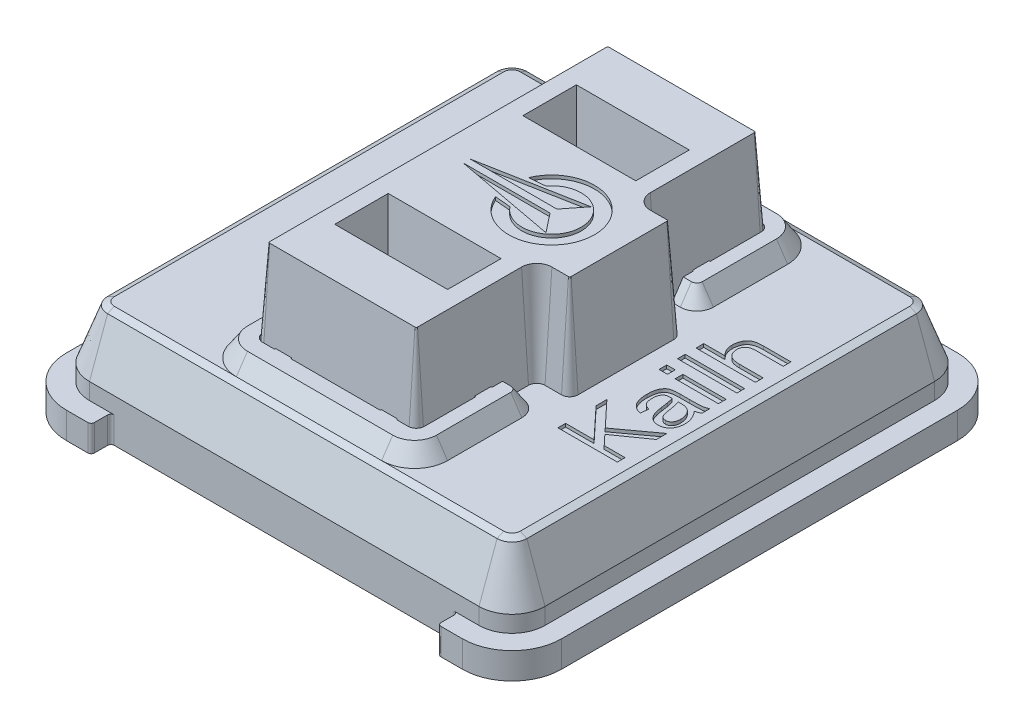
SolidWorks part; units mm, degrees
material "Plastique personnalisé"
ref_plane "Front Plane" through (0, 0, 0) normal (0, 0, 1) x (1, 0, 0)
ref_plane "Top Plane" through (0, 0, 0) normal (0, 1, 0) x (1, 0, 0)
ref_plane "Right Plane" through (0, 0, 0) normal (1, 0, 0) x (0, 0, -1)
sketch "Sketch1" plane through (0, 0, 0) normal (0, 1, 0) x (1, 0, 0)
  line L0 (-12.6999, -17.2743) -> (27.7413, -17.2743) construction
  line L1 (-6, 7.5) -> (6, 7.5)
  line L2 (-7.5, 6) -> (-7.5, -6)
  line L3 (-6, -7.5) -> (6, -7.5)
  line L4 (7.5, 6) -> (7.5, -6)
  line L5 (-7.5, 7.5) -> (7.5, -7.5) construction
  line L6 (-7.5, -7.5) -> (7.5, 7.5) construction
  arc A0 (-7.5, -6) -> (-6, -7.5) centre (-6, -6) ccw
  arc A1 (6, -7.5) -> (7.5, -6) centre (6, -6) ccw
  arc A2 (6, 7.5) -> (7.5, 6) centre (6, 6) cw
  arc A3 (-6, 7.5) -> (-7.5, 6) centre (-6, 6) ccw
  point P0 (0, 0)
  dimension "D3" = 1.5
  dimension "D1" = 15
  dimension "D2" = 15
sketch "Sketch5" plane through (0, 0, 0) normal (0, 1, 0) x (1, 0, 0)
  line L1 (6, -7.5) -> (-6, -7.5)
  line L2 (7.5, -6) -> (7.5, 6)
  line L3 (6, 7.5) -> (-6, 7.5)
  line L4 (-7.5, -6) -> (-7.5, 6)
  line L5 (7.5, -7.5) -> (-7.5, 7.5) construction
  line L6 (7.5, 7.5) -> (-7.5, -7.5) construction
  arc A0 (-6, -7.5) -> (-7.5, -6) centre (-6, -6) cw
  arc A1 (6, -7.5) -> (7.5, -6) centre (6, -6) ccw
  arc A2 (7.5, 6) -> (6, 7.5) centre (6, 6) ccw
  arc A3 (-6, 7.5) -> (-7.5, 6) centre (-6, 6) ccw
  point P0 (0, 0)
  dimension "D1" = 1.5
extrude "Boss-Extrude4" add sketch "Sketch5" along normal mid plane 0.8
sketch "Sketch6" plane through (0, 0.4, 0) normal (0, 1, 0) x (1, 0, 0)
  line L0 (-7.5, 7.5) -> (7.5, -7.5) construction
  line L1 (5.9, -6.9) -> (-5.9, -6.9)
  line L2 (6.9, -5.9) -> (6.9, 5.9)
  line L3 (5.9, 6.9) -> (-5.9, 6.9)
  line L4 (-6.9, -5.9) -> (-6.9, 5.9)
  line L5 (6.9, -6.9) -> (-6.9, 6.9) construction
  line L6 (6.9, 6.9) -> (-6.9, -6.9) construction
  arc A0 (-5.9, -6.9) -> (-6.9, -5.9) centre (-5.9, -5.9) cw
  arc A1 (5.9, -6.9) -> (6.9, -5.9) centre (5.9, -5.9) ccw
  arc A2 (6.9, 5.9) -> (5.9, 6.9) centre (5.9, 5.9) ccw
  arc A3 (-5.9, 6.9) -> (-6.9, 5.9) centre (-5.9, 5.9) ccw
  point P0 (0, 0)
  dimension "D2" = 1
  dimension "D1" = 13.8
extrude "Boss-Extrude5" add sketch "Sketch6" along normal blind 0.5
sketch "Sketch7" plane through (0, 0.9, 0) normal (0, 1, 0) x (1, 0, 0)
  line L4 (-5.9, -6.9) -> (5.9, -6.9)
  line L5 (6.9, -5.9) -> (6.9, 5.9)
  line L6 (5.9, 6.9) -> (-5.9, 6.9)
  line L7 (-6.9, 5.9) -> (-6.9, -5.9)
  line L8 (-5.9, -6.9) -> (5.9, -6.9)
  line L9 (6.9, -5.9) -> (6.9, 5.9)
  line L10 (5.9, 6.9) -> (-5.9, 6.9)
  line L11 (-6.9, 5.9) -> (-6.9, -5.9)
  arc A4 (-6.9, -5.9) -> (-5.9, -6.9) centre (-5.9, -5.9) ccw
  arc A5 (5.9, -6.9) -> (6.9, -5.9) centre (5.9, -5.9) ccw
  arc A6 (6.9, 5.9) -> (5.9, 6.9) centre (5.9, 5.9) ccw
  arc A7 (-5.9, 6.9) -> (-6.9, 5.9) centre (-5.9, 5.9) ccw
  arc A8 (-6.9, -5.9) -> (-5.9, -6.9) centre (-5.9, -5.9) ccw
  arc A9 (5.9, -6.9) -> (6.9, -5.9) centre (5.9, -5.9) ccw
  arc A10 (6.9, 5.9) -> (5.9, 6.9) centre (5.9, 5.9) ccw
  arc A11 (-5.9, 6.9) -> (-6.9, 5.9) centre (-5.9, 5.9) ccw
  arc M9 (-6.9, -5.9) -> (-5.9, -6.9) centre (-5.9, -5.9) ccw
  line M10 (-5.9, -6.9) -> (5.9, -6.9)
  arc M11 (5.9, -6.9) -> (6.9, -5.9) centre (5.9, -5.9) ccw
  line M12 (6.9, -5.9) -> (6.9, 5.9)
  arc M13 (6.9, 5.9) -> (5.9, 6.9) centre (5.9, 5.9) ccw
  line M14 (5.9, 6.9) -> (-5.9, 6.9)
  arc M15 (-5.9, 6.9) -> (-6.9, 5.9) centre (-5.9, 5.9) ccw
  line M16 (-6.9, 5.9) -> (-6.9, -5.9)
  dimension "D1" = 0
extrude "Boss-Extrude6" add sketch "Sketch7" along normal offset from surface 2.5 draft 20 contours M16 M9 M10 M11 M12 M13 M14 M15
chamfer "Chamfer1" distance 0.1 angle 45 8 edges at (0, 2.5, -6.3176) (6.1953, 2.5, -6.1953) (6.3176, 2.5, 0) (6.1953, 2.5, 6.1953) (0, 2.5, 6.3176) (-6.1953, 2.5, 6.1953) (-6.3176, 2.5, 0) (-6.1953, 2.5, -6.1953)
sketch "Sketch8" plane through (0, 2.5, 0) normal (0, 1, 0) x (1, 0, 0)
  line L0 (5.9, 6.1503) -> (-5.9, 6.1503) construction
  line L1 (2.2, -6.1503) -> (-2.2, -6.1503)
  line L2 (3.2, -5.1503) -> (3.2, -2.9003)
  line L3 (2.2, 6.1503) -> (-2.2, 6.1503)
  line L4 (-3.2, -5.1503) -> (-3.2, 5.1503)
  line L5 (3.2, -6.1503) -> (-3.2, 6.1503) construction
  line L6 (3.2, 6.1503) -> (-3.2, -6.1503) construction
  line L7 (2.7, 2.4003) -> (2.3, 2.4003)
  line L8 (2.3, 2.4003) -> (2.3, -2.4003)
  line L9 (2.3, -2.4003) -> (2.7, -2.4003)
  line L10 (3.2, 2.9003) -> (3.2, 5.1503)
  arc A0 (-2.2, -6.1503) -> (-3.2, -5.1503) centre (-2.2, -5.1503) cw
  arc A1 (2.2, -6.1503) -> (3.2, -5.1503) centre (2.2, -5.1503) ccw
  arc A2 (3.2, 5.1503) -> (2.2, 6.1503) centre (2.2, 5.1503) ccw
  arc A3 (-2.2, 6.1503) -> (-3.2, 5.1503) centre (-2.2, 5.1503) ccw
  arc A4 (2.7, -2.4003) -> (3.2, -2.9003) centre (2.7, -2.9003) cw
  arc A5 (2.7, 2.4003) -> (3.2, 2.9003) centre (2.7, 2.9003) ccw
  point P0 (0, 0)
  point P28 (3.2, 2.4003)
  dimension "D2" = 1
  dimension "D5" = 0.5
  dimension "D1" = 6.4
  dimension "D3" = 3.75
  dimension "D4" = 0.9
extrude "Boss-Extrude7" add sketch "Sketch8" along normal blind 0.5 draft 34
sketch "Sketch9" plane through (0, 2.5, 0) normal (0, 1, 0) x (1, 0, 0)
  line L1 (-2.2, -5.35) -> (2.2, -5.35)
  line L2 (-2.45, -5.1) -> (-2.45, 5.1)
  line L3 (-2.2, 5.35) -> (2.2, 5.35)
  line L4 (2.45, -5.1) -> (2.45, 5.1)
  line L5 (-2.45, -5.35) -> (2.45, 5.35) construction
  line L6 (-2.45, 5.35) -> (2.45, -5.35) construction
  arc A0 (-2.2, -5.35) -> (-2.45, -5.1) centre (-2.2, -5.1) cw
  arc A1 (2.2, -5.35) -> (2.45, -5.1) centre (2.2, -5.1) ccw
  arc A2 (2.2, 5.35) -> (2.45, 5.1) centre (2.2, 5.1) cw
  arc A3 (-2.45, 5.1) -> (-2.2, 5.35) centre (-2.2, 5.1) cw
  point P0 (0, 0)
  dimension "D2" = 0.25
  dimension "D1" = 10.7
  dimension "D3" = 4.9
extrude "Cut-Extrude1" cut sketch "Sketch9" along normal through all
sketch "Sketch11" plane through (0, 2.5, 0) normal (0, 1, 0) x (1, 0, 0)
  line L0 (2.2, 5.35) -> (-2.2, 5.35) construction
  line L1 (2.45, 2.7376) -> (2.45, 5.1) construction
  line L2 (-2.45, 5.1) -> (-2.45, -5.1) construction
  line L3 (-2.2, -5.35) -> (2.2, -5.35) construction
  line L4 (2.45, -5.1) -> (2.45, -2.7376) construction
  line L5 (-1.8598, 5.35) -> (-1.3402, 5.35)
  line L6 (1.3402, 5.35) -> (1.8598, 5.35)
  line L7 (2.45, 3.5598) -> (2.45, 3.0402)
  line L8 (2.45, -3.0402) -> (2.45, -3.5598)
  line L9 (1.8598, -5.35) -> (1.3402, -5.35)
  line L10 (-1.3402, -5.35) -> (-1.8598, -5.35)
  line L11 (-2.45, -3.5598) -> (-2.45, -3.0402)
  line L12 (-2.45, 3.0402) -> (-2.45, 3.5598)
  line L13 (0, 0) -> (-1.4423, 0) construction
  line L14 (0, 0) -> (0, 1.7321) construction
  arc A0 (-1.8598, 5.35) -> (-1.3402, 5.35) centre (-1.6, 5.5) ccw
  arc A1 (1.3402, 5.35) -> (1.8598, 5.35) centre (1.6, 5.5) ccw
  arc A2 (2.45, 3.5598) -> (2.45, 3.0402) centre (2.6, 3.3) ccw
  arc A3 (-2.45, 3.5598) -> (-2.45, 3.0402) centre (-2.6, 3.3) cw
  arc A4 (-2.45, -3.0402) -> (-2.45, -3.5598) centre (-2.6, -3.3) cw
  arc A5 (-1.8598, -5.35) -> (-1.3402, -5.35) centre (-1.6, -5.5) cw
  arc A6 (1.3402, -5.35) -> (1.8598, -5.35) centre (1.6, -5.5) cw
  arc A7 (2.45, -3.0402) -> (2.45, -3.5598) centre (2.6, -3.3) ccw
  dimension "D1" = 0.3
  dimension "D2" = 0.15
  dimension "D3" = 1.6
  dimension "D4" = 3.3
extrude "Boss-Extrude8" add sketch "Sketch11" along normal up to surface (0.5 mm away) up to face at (0.7315, 3, 0)
sketch "Sketch12" plane through (0, 2.5, 0) normal (0, 1, 0) x (1, 0, 0)
  line L0 (2.7, 1.7) -> (3.2, 1.7)
  line L1 (2.2, 5.35) -> (-2.2, 5.35)
  line L2 (2.45, 5.1) -> (2.45, 1.95)
  line L3 (2.2, -5.35) -> (-2.2, -5.35)
  line L4 (-2.45, 5.1) -> (-2.45, -5.1)
  line L5 (2.45, 5.35) -> (-2.45, -5.35) construction
  line L6 (2.45, -5.35) -> (-2.45, 5.35) construction
  line L7 (3.45, 1.45) -> (3.45, -1.45)
  line L8 (3.2, -1.7) -> (2.7, -1.7)
  line L9 (2.45, -1.95) -> (2.45, -5.1)
  line L10 (-1.5, -2.25) -> (1.5, -3.45) construction
  line L11 (-1.5, -2.25) -> (1.5, -2.25)
  line L12 (-1.5, -2.25) -> (-1.5, -3.45)
  line L13 (-1.5, -3.45) -> (1.5, -3.45)
  line L14 (1.5, -2.25) -> (1.5, -3.45)
  line L15 (0, 0) -> (-1.3542, 0) construction
  line L16 (1.5, 2.25) -> (1.5, 3.45)
  line L17 (-1.5, 3.45) -> (1.5, 3.45)
  line L18 (-1.5, 2.25) -> (-1.5, 3.45)
  line L19 (-1.5, 2.25) -> (1.5, 2.25)
  arc A0 (-2.2, -5.35) -> (-2.45, -5.1) centre (-2.2, -5.1) cw
  arc A1 (2.45, -5.1) -> (2.2, -5.35) centre (2.2, -5.1) cw
  arc A2 (2.7, -1.7) -> (2.45, -1.95) centre (2.7, -1.95) ccw
  arc A3 (-2.2, 5.35) -> (-2.45, 5.1) centre (-2.2, 5.1) ccw
  arc A4 (2.2, 5.35) -> (2.45, 5.1) centre (2.2, 5.1) cw
  arc A5 (2.7, 1.7) -> (2.45, 1.95) centre (2.7, 1.95) cw
  arc A6 (3.2, 1.7) -> (3.45, 1.45) centre (3.2, 1.45) cw
  arc A7 (3.45, -1.45) -> (3.2, -1.7) centre (3.2, -1.45) cw
  point P0 (0, 0)
  point P18 (2.45, -1.7)
  point P29 (3.45, 1.7)
  point P32 (3.45, -1.7)
  point P37 (0, -2.85)
  dimension "D5" = 0.25
  dimension "D1" = 4.9
  dimension "D2" = 10.7
  dimension "D3" = 1
  dimension "D4" = 3.4
  dimension "D6" = 1.2
  dimension "D7" = 3
  dimension "D8" = 5.7
extrude "Boss-Extrude9" add sketch "Sketch12" along normal blind 3 draft 4
sketch "Sketch13" plane through (0, 2.5, 0) normal (0, 1, 0) x (1, 0, 0)
  line L0 (5.809, 2.994) -> (5.809, -2.994) construction
  line L1 (5.809, 0) -> (0, 0) construction
  text T0 "Kailh" font "@Arial Unicode MS" height 1.8
extrude "Cut-Extrude2" cut sketch "Sketch13" against normal blind 0.1
sketch "Sketch14" plane through (0, 5.5, 0) normal (0, 1, 0) x (1, 0, 0)
  line L0 (0, 0.5) -> (0.4816, 0.5421)
  line L1 (0, -0.5) -> (0.4816, -0.5421)
  line L2 (0, 0) -> (-1.6937, 0) construction
  line L3 (-1.377, 0.1043) -> (1.2556, 0.1043)
  line L4 (1.2556, 0.1043) -> (1.7122, 0.6819)
  line L5 (1.7122, 0.6819) -> (-1.377, 0.1043)
  line L6 (1.2556, -0.1043) -> (1.7122, -0.6819)
  line L7 (-1.377, -0.1043) -> (1.2556, -0.1043)
  line L8 (1.7122, -0.6819) -> (-1.377, -0.1043)
  arc A0 (0, -0.5) -> (0, 0.5) centre (1.2, 0) ccw
  arc A1 (0.4816, -0.5421) -> (0.4816, 0.5421) centre (1.2, 0) ccw
  dimension "D2" = 0.9
  dimension "D3" = 1.3
  dimension "D1" = 10
  dimension "D4" = 1.2
  dimension "D5" = 1
extrude "Cut-Extrude3" cut sketch "Sketch14" against normal blind 0.1
sketch "Sketch15" plane through (0, 0, 0) normal (0, 1, 0) x (1, 0, 0)
  line L0 (22.7981, 9.2794) -> (-33.7496, 9.2794) construction
sketch "Sketch16" plane through (0, -0.4, 0) normal (0, -1, 0) x (1, 0, 0)
  line L1 (5.9, -6.9) -> (-5.9, -6.9)
  line L2 (6.9, -5.9) -> (6.9, 5.9)
  line L3 (5.9, 6.9) -> (-5.9, 6.9)
  line L4 (-6.9, -5.9) -> (-6.9, 5.9)
  line L5 (6.9, -6.9) -> (-6.9, 6.9) construction
  line L6 (6.9, 6.9) -> (-6.9, -6.9) construction
  arc A0 (-5.9, -6.9) -> (-6.9, -5.9) centre (-5.9, -5.9) cw
  arc A1 (5.9, -6.9) -> (6.9, -5.9) centre (5.9, -5.9) ccw
  arc A2 (6.9, 5.9) -> (5.9, 6.9) centre (5.9, 5.9) ccw
  arc A3 (-6.9, 5.9) -> (-5.9, 6.9) centre (-5.9, 5.9) cw
  point P0 (0, 0)
  dimension "D2" = 1
  dimension "D1" = 13.8
extrude "Boss-Extrude10" add sketch "Sketch16" along normal blind 1.3
sketch "Sketch17" plane through (0, -1.7, 0) normal (0, -1, 0) x (1, 0, 0)
  line L4 (-5.9, -6.9) -> (5.9, -6.9)
  line L5 (6.9, -5.9) -> (6.9, 5.9)
  line L6 (5.9, 6.9) -> (-5.9, 6.9)
  line L7 (-6.9, 5.9) -> (-6.9, -5.9)
  line L8 (-5.9, -6.9) -> (5.9, -6.9)
  line L9 (6.9, -5.9) -> (6.9, 5.9)
  line L10 (5.9, 6.9) -> (-5.9, 6.9)
  line L11 (-6.9, 5.9) -> (-6.9, -5.9)
  arc A4 (-6.9, -5.9) -> (-5.9, -6.9) centre (-5.9, -5.9) ccw
  arc A5 (5.9, -6.9) -> (6.9, -5.9) centre (5.9, -5.9) ccw
  arc A6 (6.9, 5.9) -> (5.9, 6.9) centre (5.9, 5.9) ccw
  arc A7 (-5.9, 6.9) -> (-6.9, 5.9) centre (-5.9, 5.9) ccw
  arc A8 (-6.9, -5.9) -> (-5.9, -6.9) centre (-5.9, -5.9) ccw
  arc A9 (5.9, -6.9) -> (6.9, -5.9) centre (5.9, -5.9) ccw
  arc A10 (6.9, 5.9) -> (5.9, 6.9) centre (5.9, 5.9) ccw
  arc A11 (-5.9, 6.9) -> (-6.9, 5.9) centre (-5.9, 5.9) ccw
  dimension "D1" = 0
extrude "Boss-Extrude11" add sketch "Sketch17" along normal blind 0.9 draft 25
sketch "Sketch18" plane through (0, -2.6, 0) normal (0, -1, 0) x (1, 0, 0)
  line L1 (-6.275, 2.5) -> (-3.125, 2.5)
  line L2 (-6.275, 2.5) -> (-6.275, -2.5)
  line L3 (-6.275, -2.5) -> (-3.125, -2.5)
  line L4 (-3.125, 2.5) -> (-3.125, -2.5)
  line L5 (-6.275, 2.5) -> (-3.125, -2.5) construction
  line L6 (-6.275, -2.5) -> (-3.125, 2.5) construction
  point P0 (-4.7, 0)
  dimension "D1" = 3.15
  dimension "D2" = 5
  dimension "D3" = 4.7
extrude "Cut-Extrude4" cut sketch "Sketch18" against normal blind 4
sketch "Sketch19" plane through (0, -2.6, 0) normal (0, -1, 0) x (1, 0, 0)
  line L0 (0, 0) -> (2.7131, 0) construction
  circle A0 centre (0, 0) radius 1.6
  circle A1 centre (0, 5.5) radius 0.9
  circle A3 centre (0, -5.5) radius 0.9
  dimension "D1" = 3.2
  dimension "D3" = 1.8
  dimension "D2" = 11
extrude "Boss-Extrude12" add sketch "Sketch19" along normal blind 2.65
chamfer "Chamfer2" distance 0.5 angle 45 3 edges at (0, -5.25, -4.6) (0, -5.25, -1.6) (0, -5.25, 4.6)
sketch "Sketch20" plane through (0, -2.6, 0) normal (0, -1, 0) x (1, 0, 0)
  line L1 (5.725, 0.575) -> (6.075, 0.575)
  line L2 (5.725, 0.575) -> (5.725, -0.575)
  line L3 (5.725, -0.575) -> (6.075, -0.575)
  line L4 (6.075, 0.575) -> (6.075, -0.575)
  line L5 (5.725, 0.575) -> (6.075, -0.575) construction
  line L6 (5.725, -0.575) -> (6.075, 0.575) construction
  line L8 (3.55, 5.425) -> (4.05, 5.425)
  line L9 (3.55, 5.425) -> (3.55, 4.575)
  line L10 (3.55, 4.575) -> (4.05, 4.575)
  line L11 (4.05, 5.425) -> (4.05, 4.575)
  line L12 (3.55, 5.425) -> (4.05, 4.575) construction
  line L13 (3.55, 4.575) -> (4.05, 5.425) construction
  point P0 (5.9, 0)
  point P5 (3.8, 5)
  dimension "D1" = 1.15
  dimension "D2" = 0.35
  dimension "D3" = 5.9
  dimension "D4" = 0.5
  dimension "D5" = 0.85
  dimension "D6" = 5
  dimension "D7" = 3.8
extrude "Boss-Extrude13" add sketch "Sketch20" along normal blind 3
sketch "Sketch21" plane through (6.075, 0, 0) normal (1, 0, 0) x (0, 0, -1)
  line L0 (0, -5.6) -> (0, -3.8431) construction
  line L1 (0.575, -5.6) -> (-0.575, -5.6) construction
  line L2 (-5, -5.6) -> (-5, -3.8431) construction
  line L3 (-4.575, -5.6) -> (-5.425, -5.6) construction
  line L4 (-0.575, -4.8541) -> (-0.2165, -5.475)
  line L5 (-0.575, -5.6) -> (-0.575, -2.6) construction
  line L6 (0.575, -4.8541) -> (0.2165, -5.475)
  line L7 (0.575, -5.6) -> (0.575, -2.6) construction
  line L8 (-5.425, -5.2786) -> (-5.1768, -5.5268)
  line L9 (-5.425, -5.6) -> (-5.425, -2.6) construction
  line L10 (-4.575, -5.2786) -> (-4.8232, -5.5268)
  line L11 (-4.575, -5.6) -> (-4.575, -2.6) construction
  line L12 (-0.575, -4.8541) -> (-0.575, -5.7)
  line L13 (-0.575, -5.7) -> (-4.575, -5.7)
  line L14 (-4.575, -5.7) -> (-4.575, -5.2786)
  line L16 (-5.425, -5.2786) -> (-5.425, -6.7)
  line L17 (-5.425, -6.7) -> (0.575, -6.7)
  line L18 (0.575, -6.7) -> (0.575, -4.8541)
  arc A0 (-0.2165, -5.475) -> (0.2165, -5.475) centre (0, -5.35) ccw
  arc A1 (-5.1768, -5.5268) -> (-4.8232, -5.5268) centre (-5, -5.35) ccw
  dimension "D1" = 0.5
  dimension "D2" = 30
  dimension "D3" = 45
  dimension "D4" = 0.1
  dimension "D5" = 1
extrude "Cut-Extrude5" cut sketch "Sketch21" against normal up to surface (2.525 mm away) up to face at (3.55, -4.1, 5)
sketch "Sketch22" plane through (0, 0, 0) normal (1, 0, 0) x (0, 0, -1)
  line L0 (-13.7977, 33.6254) -> (-14.1977, -19.6321) construction
  line L1 (-6.9, -1.7) -> (-7.25, -1.7)
  line L2 (-7.25, -1.7) -> (-7.25, -1.95)
  line L3 (-7.25, -1.95) -> (-6.6115, -2.3186)
  line L4 (-6.4803, -2.6) -> (-6.9, -1.7) construction
  line L5 (-6.6115, -2.3186) -> (-6.9, -1.7)
  line L6 (0, 0) -> (0, -3.4947) construction
  dimension "D1" = 14.5
  dimension "D2" = 30
  dimension "D3" = 0.25
extrude "Boss-Extrude14" add sketch "Sketch22" along normal blind 3 from offset 2
mirror "Mirror1" about plane through (0, 0, 0) normal (1, 0, 0) of "Boss-Extrude14"
mirror "Mirror2" about plane through (0, 0, 0) normal (0, 0, 1) of "Mirror1", "Boss-Extrude14"
sketch "Sketch23" plane through (0, -0.4, 0) normal (0, -1, 0) x (1, 0, 0)
  line L0 (-6, 7.5) -> (6, 7.5) construction
  line L1 (-5.25, 7.5) -> (5.25, 7.5)
  line L2 (-5.25, 7.5) -> (-5.25, 6.9)
  line L3 (-5.25, 6.9) -> (5.25, 6.9)
  line L4 (5.25, 7.5) -> (5.25, 6.9)
  line L5 (5.9, 6.9) -> (5, 6.9) construction
  line L6 (0, 0) -> (0, 6.9) construction
  line L7 (2, 6.9) -> (-2, 6.9) construction
  line L8 (0, 0) -> (-4.2254, 0) construction
  line L9 (5.25, -7.5) -> (5.25, -6.9)
  line L10 (-5.25, -6.9) -> (5.25, -6.9)
  line L11 (-5.25, -7.5) -> (-5.25, -6.9)
  line L12 (-5.25, -7.5) -> (5.25, -7.5)
  dimension "D1" = 10.5
extrude "Cut-Extrude6" cut sketch "Sketch23" against normal up to next
fillet "Fillet1" radius 0.1 8 edges at (-5.25, 0, 6.9) (5.25, 0, 6.9) (5.25, 0, -6.9) (-5.25, 0, -6.9) (-5.25, 0, -7.5) (5.25, 0, -7.5) (5.25, 0, 7.5) (-5.25, 0, 7.5)
sketch "Esquisse1" plane through (0, -0.4, 0) normal (0, -1, 0) x (1, 0, 0)
  line L1 (8.3441, -7.5837) -> (-8.2399, -7.5837)
  line L2 (8.3441, -7.5837) -> (8.3441, 7.9691)
  line L3 (8.3441, 7.9691) -> (-8.2399, 7.9691)
  line L4 (-8.2399, -7.5837) -> (-8.2399, 7.9691)
extrude "Enlèv. mat.-Extru.1" cut sketch "Esquisse1" along normal blind 10
